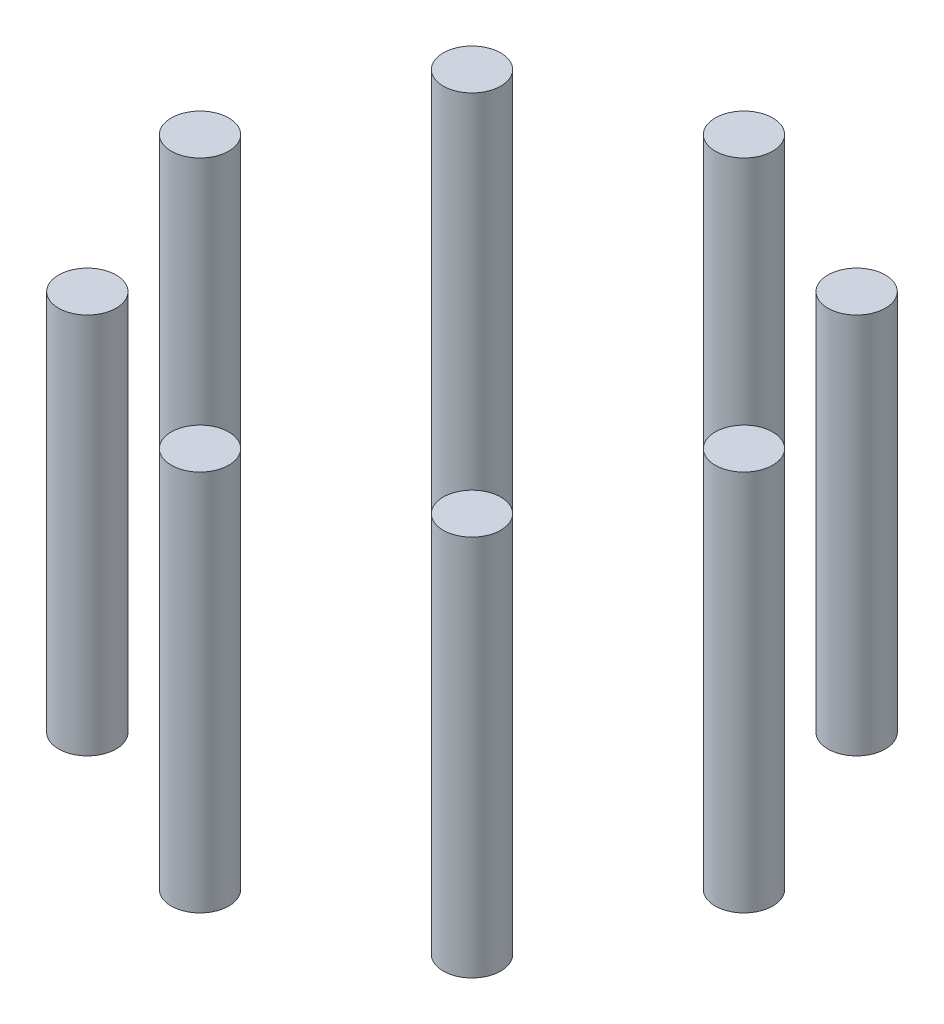
SolidWorks part; units mm, degrees
ref_plane "Front Plane" through (0, 0, 0) normal (0, 0, 1) x (1, 0, 0)
ref_plane "Top Plane" through (0, 0, 0) normal (0, 1, 0) x (1, 0, 0)
ref_plane "Right Plane" through (0, 0, 0) normal (1, 0, 0) x (0, 0, -1)
sketch "Sketch1" plane through (0, 0, 0) normal (0, 1, 0) x (1, 0, 0)
  circle A0 centre (0, 0) radius 52
  circle A1 centre (-52, 0) radius 5.5
  circle A2 centre (-36.7696, 36.7696) radius 5.5
  circle A3 centre (0, 52) radius 5.5
  circle A4 centre (36.7696, 36.7696) radius 5.5
  circle A5 centre (52, 0) radius 5.5
  circle A6 centre (36.7696, -36.7696) radius 5.5
  circle A7 centre (0, -52) radius 5.5
  circle A8 centre (-36.7696, -36.7696) radius 5.5
  point P21 (0, 0)
  dimension "D1" = 8
extrude "Boss-Extrude1" add sketch "Sketch1" along normal blind 73 contours A1 | A8 | A2 | A3 | A4 | A5 | A6 | A7
